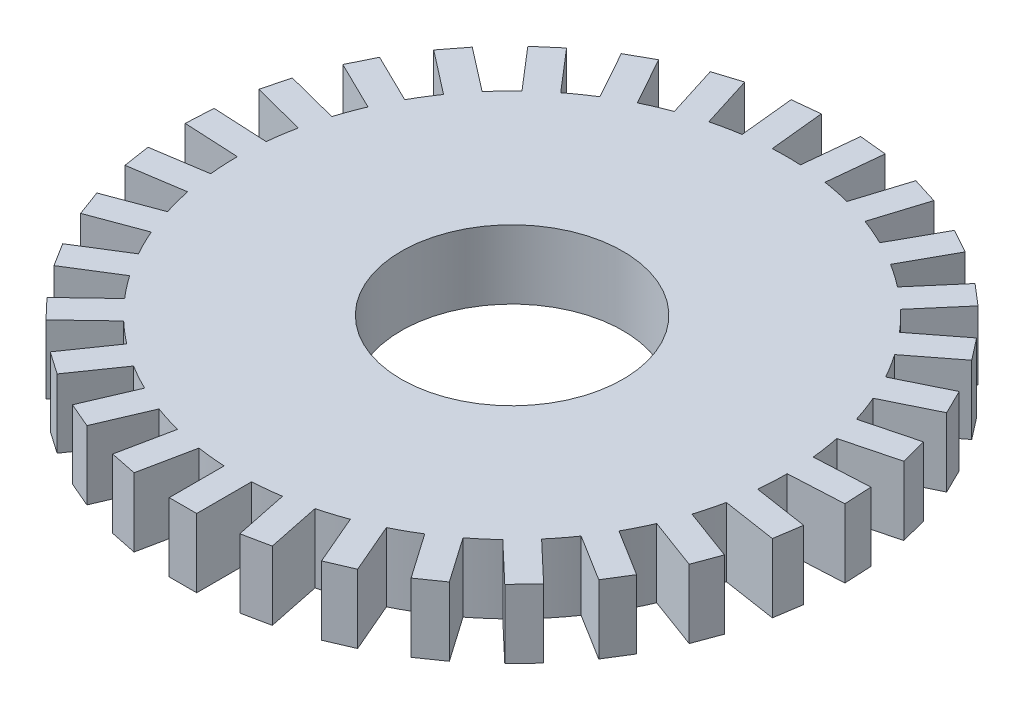
SolidWorks part; units mm, degrees
ref_plane "Front Plane" through (0, 0, 0) normal (0, 0, 1) x (1, 0, 0)
ref_plane "Top Plane" through (0, 0, 0) normal (0, 1, 0) x (1, 0, 0)
ref_plane "Right Plane" through (0, 0, 0) normal (1, 0, 0) x (0, 0, -1)
sketch "Sketch1" plane through (0, 0, 0) normal (0, 1, 0) x (1, 0, 0)
  line L0 (-0.6398, 2.4581) -> (-0.8821, 2.3819)
  line L1 (-0.6398, 2.4581) -> (-0.7922, 2.9427)
  line L2 (-0.8821, 2.3819) -> (-1.0345, 2.8665)
  line L3 (-0.7922, 2.9427) -> (-1.0345, 2.8665)
  line L4 (-0.1319, 2.5366) -> (-0.1836, 3.0419)
  line L5 (-0.3846, 2.5107) -> (-0.4363, 3.0161)
  line L6 (-0.1836, 3.0419) -> (-0.4363, 3.0161)
  line L7 (0.3814, 2.5112) -> (0.4325, 3.0166)
  line L8 (0.1287, 2.5367) -> (0.1798, 3.0422)
  line L9 (0.4325, 3.0166) -> (0.1798, 3.0422)
  line L10 (0.8791, 2.383) -> (1.0309, 2.8678)
  line L11 (0.6367, 2.4589) -> (0.7885, 2.9437)
  line L12 (1.0309, 2.8678) -> (0.7885, 2.9437)
  line L13 (1.3408, 2.1573) -> (1.5871, 2.6016)
  line L14 (1.1187, 2.2804) -> (1.3649, 2.7247)
  line L15 (1.5871, 2.6016) -> (1.3649, 2.7247)
  line L16 (1.7476, 1.8432) -> (2.0783, 2.2289)
  line L17 (1.5548, 2.0085) -> (1.8855, 2.3942)
  line L18 (2.0783, 2.2289) -> (1.8855, 2.3942)
  line L19 (2.0829, 1.4537) -> (2.4844, 1.7649)
  line L20 (1.9273, 1.6544) -> (2.3288, 1.9656)
  line L21 (2.4844, 1.7649) -> (2.3288, 1.9656)
  line L22 (2.3329, 1.0046) -> (2.7888, 1.2286)
  line L23 (2.2209, 1.2326) -> (2.6768, 1.4566)
  line L24 (2.7888, 1.2286) -> (2.6768, 1.4566)
  line L25 (2.4874, 0.5145) -> (2.9791, 0.6421)
  line L26 (2.4235, 0.7603) -> (2.9152, 0.888)
  line L27 (2.9791, 0.6421) -> (2.9152, 0.888)
  line L28 (2.54, 0.0032) -> (3.0473, 0.0293)
  line L29 (2.527, 0.2569) -> (3.0343, 0.283)
  line L30 (3.0473, 0.0293) -> (3.0343, 0.283)
  line L31 (2.4887, -0.5081) -> (2.9908, -0.5847)
  line L32 (2.527, -0.257) -> (3.0292, -0.3336)
  line L33 (2.9908, -0.5847) -> (3.0292, -0.3336)
  line L34 (2.3354, -0.9987) -> (2.8119, -1.1748)
  line L35 (2.4235, -0.7604) -> (2.9, -0.9366)
  line L36 (2.8119, -1.1748) -> (2.9, -0.9366)
  line L37 (2.0866, -1.4484) -> (2.5179, -1.7168)
  line L38 (2.2208, -1.2327) -> (2.6521, -1.5012)
  line L39 (2.5179, -1.7168) -> (2.6521, -1.5012)
  line L40 (1.7523, -1.8387) -> (2.1207, -2.1885)
  line L41 (1.9272, -1.6545) -> (2.2956, -2.0043)
  line L42 (2.1207, -2.1885) -> (2.2956, -2.0043)
  line L43 (1.3463, -2.1538) -> (1.6368, -2.5706)
  line L44 (1.5547, -2.0086) -> (1.8452, -2.4254)
  line L45 (1.6368, -2.5706) -> (1.8452, -2.4254)
  line L46 (0.8852, -2.3808) -> (1.0858, -2.8475)
  line L47 (1.1185, -2.2805) -> (1.3192, -2.7472)
  line L48 (1.0858, -2.8475) -> (1.3192, -2.7472)
  line L49 (0.3878, -2.5102) -> (0.4904, -3.0078)
  line L50 (0.6366, -2.4589) -> (0.7392, -2.9565)
  line L51 (0.4904, -3.0078) -> (0.7392, -2.9565)
  line L52 (-0.1254, -2.5369) -> (-0.1251, -3.0449)
  line L53 (0.1286, -2.5367) -> (0.1289, -3.0447)
  line L54 (-0.1251, -3.0449) -> (0.1289, -3.0447)
  line L55 (-0.6335, -2.4597) -> (-0.7355, -2.9574)
  line L56 (-0.3847, -2.5107) -> (-0.4866, -3.0084)
  line L57 (-0.7355, -2.9574) -> (-0.4866, -3.0084)
  line L58 (-1.1157, -2.2818) -> (-1.3157, -2.7488)
  line L59 (-0.8822, -2.3819) -> (-1.0823, -2.8488)
  line L60 (-1.3157, -2.7488) -> (-1.0823, -2.8488)
  line L61 (-1.5522, -2.0106) -> (-1.8421, -2.4277)
  line L62 (-1.3436, -2.1555) -> (-1.6336, -2.5727)
  line L63 (-1.8421, -2.4277) -> (-1.6336, -2.5727)
  line L64 (-1.9251, -1.6569) -> (-2.2931, -2.0072)
  line L65 (-1.75, -1.8409) -> (-2.118, -2.1912)
  line L66 (-2.2931, -2.0072) -> (-2.118, -2.1912)
  line L67 (-2.2193, -1.2355) -> (-2.6502, -1.5045)
  line L68 (-2.0848, -1.451) -> (-2.5157, -1.72)
  line L69 (-2.6502, -1.5045) -> (-2.5157, -1.72)
  line L70 (-2.4225, -0.7635) -> (-2.8988, -0.9402)
  line L71 (-2.3342, -1.0016) -> (-2.8104, -1.1783)
  line L72 (-2.8988, -0.9402) -> (-2.8104, -1.1783)
  line L73 (-2.5266, -0.2602) -> (-3.0287, -0.3374)
  line L74 (-2.488, -0.5112) -> (-2.9901, -0.5885)
  line L75 (-3.0287, -0.3374) -> (-2.9901, -0.5885)
  line L76 (-2.5273, 0.2537) -> (-3.0347, 0.2792)
  line L77 (-2.54, 0.0001) -> (-3.0474, 0.0255)
  line L78 (-3.0347, 0.2792) -> (-3.0474, 0.0255)
  line L79 (-2.4245, 0.7573) -> (-2.9163, 0.8843)
  line L80 (-2.488, 0.5114) -> (-2.9799, 0.6384)
  line L81 (-2.9163, 0.8843) -> (-2.9799, 0.6384)
  line L82 (-2.2224, 1.2298) -> (-2.6786, 1.4533)
  line L83 (-2.3341, 1.0017) -> (-2.7904, 1.2252)
  line L84 (-2.6786, 1.4533) -> (-2.7904, 1.2252)
  line L85 (-1.9294, 1.652) -> (-2.3313, 1.9627)
  line L86 (-2.0847, 1.4511) -> (-2.4866, 1.7618)
  line L87 (-2.3313, 1.9627) -> (-2.4866, 1.7618)
  line L88 (-1.5573, 2.0066) -> (-1.8884, 2.3918)
  line L89 (-1.7499, 1.841) -> (-2.0811, 2.2263)
  line L90 (-1.8884, 2.3918) -> (-2.0811, 2.2263)
  line L91 (-1.1215, 2.279) -> (-1.3683, 2.723)
  line L92 (-1.3435, 2.1556) -> (-1.5903, 2.5996)
  line L93 (-1.3683, 2.723) -> (-1.5903, 2.5996)
  circle A0 centre (0, 0) radius 3.175
  circle A1 centre (0, 0) radius 2.54
  circle A2 centre (0, 0) radius 2.54
  circle A3 centre (0, 0) radius 2.54
  circle A4 centre (0, 0) radius 2.54
  circle A5 centre (0, 0) radius 2.54
  circle A6 centre (0, 0) radius 2.54
  circle A7 centre (0, 0) radius 2.54
  circle A8 centre (0, 0) radius 2.54
  circle A9 centre (0, 0) radius 2.54
  circle A10 centre (0, 0) radius 2.54
  circle A11 centre (0, 0) radius 2.54
  circle A12 centre (0, 0) radius 2.54
  circle A13 centre (0, 0) radius 2.54
  circle A14 centre (0, 0) radius 2.54
  circle A15 centre (0, 0) radius 2.54
  circle A16 centre (0, 0) radius 2.54
  circle A17 centre (0, 0) radius 2.54
  circle A18 centre (0, 0) radius 2.54
  circle A19 centre (0, 0) radius 2.54
  circle A20 centre (0, 0) radius 2.54
  circle A21 centre (0, 0) radius 2.54
  circle A22 centre (0, 0) radius 2.54
  circle A23 centre (0, 0) radius 2.54
  circle A24 centre (0, 0) radius 2.54
  circle A25 centre (0, 0) radius 2.54
  circle A26 centre (0, 0) radius 2.54
  circle A27 centre (0, 0) radius 2.54
  circle A28 centre (0, 0) radius 2.54
  circle A29 centre (0, 0) radius 2.54
  circle A30 centre (0, 0) radius 2.54
  circle A31 centre (0, 0) radius 2.54
  point P161 (0, 0)
  dimension "D1" = 6.35
  dimension "D2" = 5.08
  dimension "D3" = 0.508
  dimension "D4" = 0.254
  dimension "D5" = 31
extrude "Boss-Extrude4" add sketch "Sketch1" along normal blind 0.635 contours A1 L0 | A1 L1 L3 L2 | L0 A1 | A1 L4 L6 L5 | A1 L7 L9 L8 | A1 L10 L12 L11 | A1 L13 L15 L14 | A1 L16 L18 L17 | A1 L19 L21 L20 | A1 L22 L24 L23 | A1 L25 L27 L26 | A1 L28 L30 L29 | A1 L31 L33 L32 | A1 L34 L36 L35 | A1 L37 L39 L38 | A1 L40 L42 L41 | A1 L43 L45 L44 | A1 L46 L48 L47 | A1 L49 L51 L50 | A1 L52 L54 L53 | A1 L55 L57 L56 | A1 L58 L60 L59 | A1 L61 L63 L62 | A1 L64 L66 L65 | A1 L67 L69 L68 | A1 L70 L72 L71 | A1 L73 L75 L74 | A1 L76 L78 L77 | A1 L79 L81 L80 | A1 L82 L84 L83 | A1 L85 L87 L86 | A1 L88 L90 L89 | A1 L91 L93 L92
sketch "Sketch2" plane through (0, 0.635, 0) normal (0, 1, 0) x (1, 0, 0)
  circle A1 centre (0, 0) radius 1
  dimension "D1" = 2
extrude "Cut-Extrude1" cut sketch "Sketch2" against normal blind 0.635
sketch "Sketch3" plane through (0, 0.635, 0) normal (0, 1, 0) x (1, 0, 0)
  circle A0 centre (1.2121, -0.5317) radius 0.3236
  circle A2 centre (0, 0) radius 1.025
  dimension "D1" = 2.05
extrude "Cut-Extrude2" cut sketch "Sketch3" against normal blind 10 contours A2
